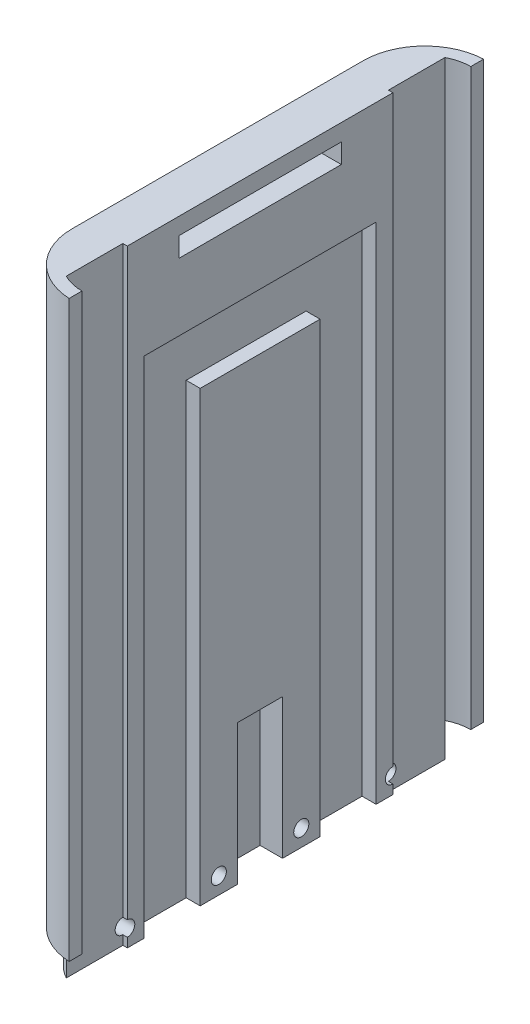
SolidWorks part; units mm, degrees
ref_plane "Front Plane" through (0, 0, 0) normal (0, 0, 1) x (1, 0, 0)
ref_plane "Top Plane" through (0, 0, 0) normal (0, 1, 0) x (1, 0, 0)
ref_plane "Right Plane" through (0, 0, 0) normal (1, 0, 0) x (0, 0, -1)
sketch "Sketch1" plane through (0, 0, 0) normal (0, 1, 0) x (1, 0, 0)
  line L0 (-45.3131, -33.5853) -> (-45.3131, -31.2966)
  line L1 (-53.3131, -23.2966) -> (-53.3131, 30.1034)
  line L2 (-45.3131, 38.1034) -> (-45.3131, 40.392)
  line L3 (-55.8131, 29.4034) -> (-55.8131, -22.5966)
  line L4 (-45.3131, 38.1034) -> (7.6869, 38.1034)
  line L5 (15.6869, 30.1034) -> (15.6869, -23.2966)
  line L6 (7.6869, -31.2966) -> (-45.3131, -31.2966)
  line L7 (-45.3131, -31.2966) -> (-45.3131, -33.5853)
  line L8 (-44.8131, -33.5966) -> (7.1869, -33.5966)
  line L9 (18.1869, -22.5966) -> (18.1869, 29.4034)
  line L10 (7.1869, 40.4034) -> (-45.3131, 40.4034)
  line L11 (-45.3131, 40.4034) -> (-45.3131, 38.1034)
  arc A0 (-53.3131, -23.2966) -> (-45.3131, -31.2966) centre (-45.3131, -23.2966) ccw
  arc A1 (-45.3131, 38.1034) -> (-53.3131, 30.1034) centre (-45.3131, 30.1034) ccw
  arc A2 (-45.3131, 40.392) -> (-55.8131, 29.4034) centre (-44.8131, 29.4034) ccw
  arc A3 (-55.8131, -22.5966) -> (-45.3131, -33.5853) centre (-44.8131, -22.5966) ccw
  arc A4 (15.6869, 30.1034) -> (7.6869, 38.1034) centre (7.6869, 30.1034) ccw
  arc A5 (7.6869, -31.2966) -> (15.6869, -23.2966) centre (7.6869, -23.2966) ccw
  arc A6 (-45.3131, -33.5853) -> (-44.8131, -33.5966) centre (-44.8131, -22.5966) ccw
  arc A7 (7.1869, -33.5966) -> (18.1869, -22.5966) centre (7.1869, -22.5966) ccw
  arc A8 (18.1869, 29.4034) -> (7.1869, 40.4034) centre (7.1869, 29.4034) ccw
extrude "Boss-Extrude1" add sketch "Sketch1" along normal blind 120 contours L3 A3 L0 A0 L1 A1 L2 A2 | L9 A8 L10 L11 L2 L4 A4 L5 A5 L6 L0 A6 L8 A7
sketch "Sketch3" plane through (0, 0, 0) normal (0, -1, 0) x (1, 0, 0)
  line L0 (-49.0131, 31.9727) -> (-49.0131, -37.6232)
  line L1 (-49.0131, -37.6232) -> (-53.3365, -34.9139)
  line L2 (-53.3365, -34.9139) -> (-55.1111, -29.9846)
  line L3 (-55.1111, -29.9846) -> (-55.1111, -26.8112)
  line L4 (-55.1111, -26.8112) -> (-55.1111, 25.4524)
  line L5 (-55.1111, 25.4524) -> (-53.6528, 27.7793)
  line L6 (-53.6528, 27.7793) -> (-52.0732, 30.2267)
  line L7 (-52.0732, 30.2267) -> (-49.0131, 31.9727)
  line L8 (11.3869, 31.9727) -> (11.3869, -38.4878)
  line L9 (11.3869, -38.4878) -> (13.2697, -37.81)
  line L10 (13.2697, -37.81) -> (16.7371, -32.277)
  line L11 (16.7371, -32.277) -> (16.5683, -31.171)
  line L12 (16.5683, -31.171) -> (16.5683, 24.7898)
  line L13 (16.5683, 24.7898) -> (15.0385, 28.9972)
  line L14 (15.0385, 28.9972) -> (11.3869, 31.9727)
  line L15 (15.6869, -30.1034) -> (15.6869, 23.2966) construction
  line L16 (-53.3131, 23.2966) -> (-53.3131, -30.1034) construction
  dimension "D1" = 4.3
  dimension "D2" = 4.3
extrude "Boss-Extrude2" add sketch "Sketch3" against normal up to surface (120 mm away) up to face at (-18.8131, 120, -3.4034)
sketch "Sketch4" plane through (0, 0, 0) normal (0, -1, 0) x (1, 0, 0)
  line L0 (11.3869, 30.3896) -> (11.3869, -37.1963) construction
  line L1 (11.3869, 20.2966) -> (10.5869, 20.2966)
  line L2 (11.3869, 20.2966) -> (11.3869, -27.1034)
  line L3 (11.3869, -27.1034) -> (10.5869, -27.1034)
  line L4 (10.5869, 20.2966) -> (10.5869, -27.1034)
  line L5 (-45.3131, -38.1034) -> (7.6869, -38.1034) construction
  line L6 (7.6869, 31.2966) -> (-45.3131, 31.2966) construction
  line L7 (-49.0131, -37.1963) -> (-49.0131, 30.3896) construction
  line L8 (-49.0131, 20.2966) -> (-48.2131, 20.2966)
  line L9 (-49.0131, 20.2966) -> (-49.0131, -27.1034)
  line L10 (-49.0131, -27.1034) -> (-48.2131, -27.1034)
  line L11 (-48.2131, 20.2966) -> (-48.2131, -27.1034)
  dimension "D1" = 0.8
  dimension "D2" = 11
  dimension "D3" = 11
  dimension "D4" = 0.8
  dimension "D5" = 11
  dimension "D6" = 11
extrude "Boss-Extrude3" add sketch "Sketch4" against normal up to surface (120 mm away) up to face at (-18.8131, 120, -3.4034)
sketch "Sketch5" plane through (0, 0, 0) normal (0, -1, 0) x (1, 0, 0)
  line L0 (-53.3131, 23.2966) -> (-53.3131, -30.1034) construction
  line L1 (15.6869, -30.1034) -> (15.6869, 23.2966) construction
  line L2 (-53.3131, 23.2966) -> (-53.3131, -30.1034)
  line L3 (15.6869, -30.1034) -> (15.6869, 23.2966)
  line L5 (-55.8131, 22.5966) -> (-55.8131, -29.4034)
  line L6 (-45.3131, -40.392) -> (-45.3131, -40.4034)
  line L7 (-45.3131, -40.4034) -> (7.1869, -40.4034)
  line L8 (18.1869, -29.4034) -> (18.1869, 22.5966)
  line L9 (7.1869, 33.5966) -> (-44.8131, 33.5966)
  line L10 (-55.8131, 22.5966) -> (-55.8131, -29.4034)
  line L11 (-45.3131, -40.392) -> (-45.3131, -40.4034)
  line L12 (-45.3131, -40.4034) -> (7.1869, -40.4034)
  line L13 (18.1869, -29.4034) -> (18.1869, 22.5966)
  line L14 (7.1869, 33.5966) -> (-44.8131, 33.5966)
  arc A0 (-45.3131, 31.2966) -> (-53.3131, 23.2966) centre (-45.3131, 23.2966) ccw construction
  arc A1 (-53.3131, -30.1034) -> (-45.3131, -38.1034) centre (-45.3131, -30.1034) ccw construction
  arc A2 (7.6869, -38.1034) -> (15.6869, -30.1034) centre (7.6869, -30.1034) ccw construction
  arc A3 (15.6869, 23.2966) -> (7.6869, 31.2966) centre (7.6869, 23.2966) ccw construction
  arc A4 (-55.8131, -29.4034) -> (-45.3131, -40.392) centre (-44.8131, -29.4034) ccw
  arc A5 (7.1869, -40.4034) -> (18.1869, -29.4034) centre (7.1869, -29.4034) ccw
  arc A6 (18.1869, 22.5966) -> (7.1869, 33.5966) centre (7.1869, 22.5966) ccw
  arc A7 (-44.8131, 33.5966) -> (-55.8131, 22.5966) centre (-44.8131, 22.5966) ccw
  arc A8 (-55.8131, -29.4034) -> (-45.3131, -40.392) centre (-44.8131, -29.4034) ccw
  arc A9 (7.1869, -40.4034) -> (18.1869, -29.4034) centre (7.1869, -29.4034) ccw
  arc A10 (18.1869, 22.5966) -> (7.1869, 33.5966) centre (7.1869, 22.5966) ccw
  arc A11 (-44.8131, 33.5966) -> (-55.8131, 22.5966) centre (-44.8131, 22.5966) ccw
  arc A12 (-45.3131, 31.2966) -> (-53.3131, 23.2966) centre (-45.3131, 23.2966) ccw
  arc A13 (-53.3131, -30.1034) -> (-45.3131, -38.1034) centre (-45.3131, -30.1034) ccw
  arc A14 (7.6869, -38.1034) -> (15.6869, -30.1034) centre (7.6869, -30.1034) ccw
  arc A15 (15.6869, 23.2966) -> (7.6869, 31.2966) centre (7.6869, 23.2966) ccw
  line M10 (11.3869, 30.3896) -> (11.3869, 20.2966)
  line M11 (11.3869, 20.2966) -> (10.5869, 20.2966)
  line M12 (10.5869, 20.2966) -> (10.5869, -27.1034)
  line M13 (10.5869, -27.1034) -> (11.3869, -27.1034)
  line M14 (11.3869, -27.1034) -> (11.3869, -37.1963)
  line M18 (-49.0131, -37.1963) -> (-49.0131, -27.1034)
  line M19 (-49.0131, -27.1034) -> (-48.2131, -27.1034)
  line M20 (-48.2131, -27.1034) -> (-48.2131, 20.2966)
  line M21 (-48.2131, 20.2966) -> (-49.0131, 20.2966)
  line M22 (-49.0131, 20.2966) -> (-49.0131, 30.3896)
  dimension "D1" = 0
extrude "Boss-Extrude4" add sketch "Sketch5" along normal blind 6 contours L2 A13 A12 M18 M19 M20 M21 M22 | L3 A15 A14 M10 M11 M12 M13 M14
sketch "Sketch6" plane through (0, -6, 0) normal (0, -1, 0) x (1, 0, 0)
  line L0 (-48.2131, -27.1034) -> (-48.2131, 20.2966) construction
  line L1 (-47.5159, 17.2966) -> (-50.7131, 17.2966)
  line L2 (-47.5159, 17.2966) -> (-47.5159, 7.2966)
  line L3 (-47.5159, 7.2966) -> (-50.7131, 7.2966)
  line L4 (-50.7131, 17.2966) -> (-50.7131, 7.2966)
  line L5 (-48.1684, -14.1034) -> (-50.7131, -14.1034)
  line L6 (-48.1684, -14.1034) -> (-48.1684, -24.1034)
  line L7 (-48.1684, -24.1034) -> (-50.7131, -24.1034)
  line L8 (-50.7131, -14.1034) -> (-50.7131, -24.1034)
  line L9 (-48.2131, 20.2966) -> (-49.0131, 20.2966) construction
  line L10 (-49.0131, -27.1034) -> (-48.2131, -27.1034) construction
  line L11 (-18.8131, 54.1571) -> (-18.8131, -72.2254)
  line L12 (-55.8131, -29.4034) -> (-55.8131, 22.5966) construction
  line L13 (10.5422, -24.1034) -> (13.0869, -24.1034)
  line L14 (13.0869, -14.1034) -> (13.0869, -24.1034)
  line L15 (10.5422, -14.1034) -> (13.0869, -14.1034)
  line L16 (10.5422, -14.1034) -> (10.5422, -24.1034)
  line L17 (9.8897, 7.2966) -> (13.0869, 7.2966)
  line L18 (13.0869, 17.2966) -> (13.0869, 7.2966)
  line L19 (9.8897, 17.2966) -> (13.0869, 17.2966)
  line L20 (9.8897, 17.2966) -> (9.8897, 7.2966)
  dimension "D1" = 2.5
  dimension "D2" = 2.5
  dimension "D3" = 10
  dimension "D4" = 10
  dimension "D5" = 3
  dimension "D6" = 3
  dimension "D7" = 37
extrude "Cut-Extrude1" cut sketch "Sketch6" against normal blind 90 contours L2 L3 L4 L1 | L6 L7 L8 L5 | L14 L13 L16 L15 | L18 L17 L20 L19
sketch "Sketch7" plane through (0, -6, 0) normal (0, -1, 0) x (1, 0, 0)
  line L1 (-45.3131, 50.3412) -> (46.0635, 50.3412)
  line L2 (-45.3131, 50.3412) -> (-45.3131, -69.8531)
  line L3 (-45.3131, -69.8531) -> (46.0635, -69.8531)
  line L4 (46.0635, 50.3412) -> (46.0635, -69.8531)
  dimension "D1" = 0
extrude "Cut-Extrude3" cut sketch "Sketch7" against normal blind 258
sketch "Sketch8" plane through (-48.2131, 0, 0) normal (1, 0, 0) x (0, 0, -1)
  line L0 (14.1034, -6) -> (-7.2966, -6) construction
  line L1 (-0.5966, 19) -> (7.4034, 19)
  line L2 (-0.5966, 19) -> (-0.5966, -11.3851)
  line L3 (-0.5966, -11.3851) -> (7.4034, -11.3851)
  line L4 (7.4034, 19) -> (7.4034, -11.3851)
  line L5 (14.1034, 84) -> (14.1034, -6) construction
  dimension "D1" = 8
  dimension "D2" = 25
  dimension "D3" = 6.7
extrude "Cut-Extrude4" cut sketch "Sketch8" against normal blind 4
sketch "Sketch9" plane through (-48.2131, 0, 0) normal (1, 0, 0) x (0, 0, -1)
  line L0 (14.1034, 84) -> (14.1034, -6) construction
  line L1 (14.1034, -6) -> (7.4034, -6) construction
  line L2 (27.1034, 120) -> (27.1034, -6) construction
  line L3 (37.1963, -6) -> (27.1034, -6) construction
  line L4 (3.392, 30.848) -> (3.392, -28.97)
  line L5 (40.392, 120) -> (40.392, 0) construction
  circle A0 centre (10.7534, -3) radius 1.35
  circle A1 centre (27.1034, -3) radius 1.35
  circle A2 centre (-20.3194, -3) radius 1.35
  circle A3 centre (-3.9694, -3) radius 1.35
  dimension "D1" = 3.35
  dimension "D2" = 3
  dimension "D3" = 2.7
  dimension "D4" = 3
  dimension "D5" = 2.7
  dimension "D6" = 37
extrude "Cut-Extrude5" cut sketch "Sketch9" against normal blind 11 contours A3 | A0 | A2 | A1
sketch "Sketch10" plane through (-55.8131, 0, 0) normal (-1, 0, 0) x (0, 0, 1)
  line L1 (-17.9034, 96) -> (11.0966, 96)
  line L2 (-17.9034, 96) -> (-17.9034, 99.5)
  line L3 (-17.9034, 99.5) -> (11.0966, 99.5)
  line L4 (11.0966, 96) -> (11.0966, 99.5)
extrude "Cut-Extrude6" cut sketch "Sketch10" against normal blind 10
sketch "Sketch11" plane through (-55.8131, 0, 0) normal (-1, 0, 0) x (0, 0, 1)
  line L0 (11.0966, 99.5) -> (-17.9034, 99.5) construction
  line L1 (-57.5597, 102.5) -> (57.5863, 102.5)
  line L2 (-57.5597, 102.5) -> (-57.5597, 128.5217)
  line L3 (-57.5597, 128.5217) -> (57.5863, 128.5217)
  line L4 (57.5863, 102.5) -> (57.5863, 128.5217)
  dimension "D1" = 3
extrude "Cut-Extrude7" cut sketch "Sketch11" against normal blind 103
sketch "Sketch12" plane through (-48.2131, 0, 0) normal (1, 0, 0) x (0, 0, -1)
  line L0 (-17.2966, 84) -> (-7.2966, 84) construction
  line L1 (-9.5952, 84) -> (18.0296, 84)
  line L2 (-9.5952, 84) -> (-9.5952, 74)
  line L3 (-9.5952, 74) -> (18.0296, 74)
  line L4 (18.0296, 84) -> (18.0296, 74)
  dimension "D1" = 10
extrude "Cut-Extrude8" cut sketch "Sketch12" against normal up to surface (2.5 mm away) up to face at (-50.7131, 39, 12.2966)
sketch "Sketch13" plane through (-55.8131, 0, 0) normal (-1, 0, 0) x (0, 0, 1)
  line L0 (-29.4034, 102.5) -> (22.5966, 102.5) construction
  line L1 (22.5966, 102.5) -> (22.5966, 0) construction
  line L2 (-29.4034, 102.5) -> (-29.4034, 0) construction
  circle A0 centre (-23.4034, 98.5) radius 1.35
  circle A1 centre (16.5966, 98.5) radius 1.35
  dimension "D1" = 4
  dimension "D2" = 6
  dimension "D3" = 2.7
  dimension "D4" = 6
  dimension "D5" = 4
  dimension "D6" = 2.7
extrude "Cut-Extrude9" cut sketch "Sketch13" against normal blind 5
